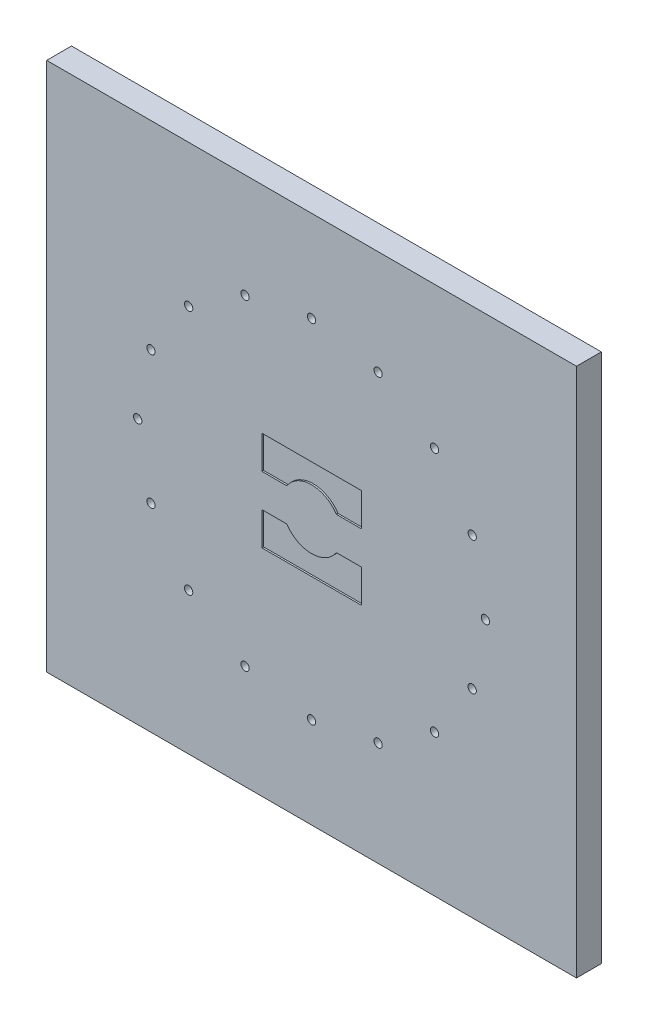
SolidWorks part; units mm, degrees
ref_plane "Plan de face" through (0, 0, 0) normal (0, 0, 1) x (1, 0, 0)
ref_plane "Plan de dessus" through (0, 0, 0) normal (0, 1, 0) x (1, 0, 0)
ref_plane "Plan de droite" through (0, 0, 0) normal (1, 0, 0) x (0, 0, -1)
sketch "Esquisse1" plane through (0, 0, 0) normal (0, 0, 1) x (1, 0, 0)
  line L1 (-16, -16) -> (16, -16)
  line L2 (-16, -16) -> (-16, 16)
  line L3 (-16, 16) -> (16, 16)
  line L4 (16, -16) -> (16, 16)
  line L5 (-16, -16) -> (16, 16) construction
  line L6 (-16, 16) -> (16, -16) construction
  point P0 (0, 0)
  dimension "D1" = 32
  dimension "D2" = 32
extrude "Boss.-Extru.1" add sketch "Esquisse1" along normal blind 1.5
sketch "Esquisse2" plane through (0, 0, 0) normal (0, 0, -1) x (-1, 0, 0)
  circle A0 centre (0, 0) radius 9.95
  circle A1 centre (0, 0) radius 10.05
  dimension "D1" = 19.9
  dimension "D2" = 20.1
extrude "Enlèv. mat.-Extru.1" cut sketch "Esquisse2" against normal blind 0.2
sketch "Esquisse3" plane through (0, 0, 0) normal (0, 0, -1) x (-1, 0, 0)
  circle A0 centre (0, 10.5) radius 0.25
  circle A1 centre (0, 0) radius 10.05 construction
  circle A2 centre (4.0182, 9.7007) radius 0.25
  circle A3 centre (7.4246, 7.4246) radius 0.25
  circle A4 centre (9.7007, 4.0182) radius 0.25
  circle A5 centre (10.5, 0) radius 0.25
  circle A6 centre (9.7007, -4.0182) radius 0.25
  circle A7 centre (7.4246, -7.4246) radius 0.25
  circle A8 centre (4.0182, -9.7007) radius 0.25
  circle A9 centre (0, -10.5) radius 0.25
  circle A10 centre (-4.0182, -9.7007) radius 0.25
  circle A11 centre (-7.4246, -7.4246) radius 0.25
  circle A12 centre (-9.7007, -4.0182) radius 0.25
  circle A13 centre (-10.5, 0) radius 0.25
  circle A14 centre (-9.7007, 4.0182) radius 0.25
  circle A15 centre (-7.4246, 7.4246) radius 0.25
  circle A16 centre (-4.0182, 9.7007) radius 0.25
  dimension "D1" = 0.5
  dimension "D2" = 10.5
  dimension "D3" = 16
extrude "Enlèv. mat.-Extru.2" cut sketch "Esquisse3" against normal through all
sketch "Esquisse4" plane through (0, 0, 0) normal (0, 0, -1) x (-1, 0, 0)
  line L1 (-15.5, -15.5) -> (15.5, -15.5)
  line L2 (-15.5, -15.5) -> (-15.5, 15.5)
  line L3 (-15.5, 15.5) -> (15.5, 15.5)
  line L4 (15.5, -15.5) -> (15.5, 15.5)
  line L5 (-15.5, -15.5) -> (15.5, 15.5) construction
  line L6 (-15.5, 15.5) -> (15.5, -15.5) construction
  point P0 (0, 0)
  dimension "D1" = 31
  dimension "D2" = 31
extrude "Enlèv. mat.-Extru.3" cut sketch "Esquisse4" against normal blind 0.1
sketch "Esquisse5" plane through (0, 0, 1.5) normal (0, 0, 1) x (1, 0, 0)
  line L0 (-3, 3) -> (3, 3)
  line L1 (3, 3) -> (3, 1)
  line L2 (3, 1) -> (1.5, 1)
  line L3 (0, 3) -> (0, 2)
  line L4 (-3, 3) -> (-3, 1)
  line L5 (-3, 1) -> (-1.5, 1)
  line L6 (-5.3732, 0) -> (8.1826, 0) construction
  line L7 (-3, -3) -> (-3, -1)
  line L8 (-3, -1) -> (-1.5, -1)
  line L9 (3, -1) -> (1.5, -1)
  line L10 (3, -3) -> (3, -1)
  line L11 (-3, -3) -> (3, -3)
  arc A0 (1.5, 1) -> (-1.5, 1) centre (0, 0) ccw
  arc A1 (1.5, -1) -> (-1.5, -1) centre (0, 0) cw
  dimension "D1" = 3
  dimension "D2" = 1.5
  dimension "D3" = 2
  dimension "D4" = 3
extrude "Enlèv. mat.-Extru.4" cut sketch "Esquisse5" against normal blind 0.1
